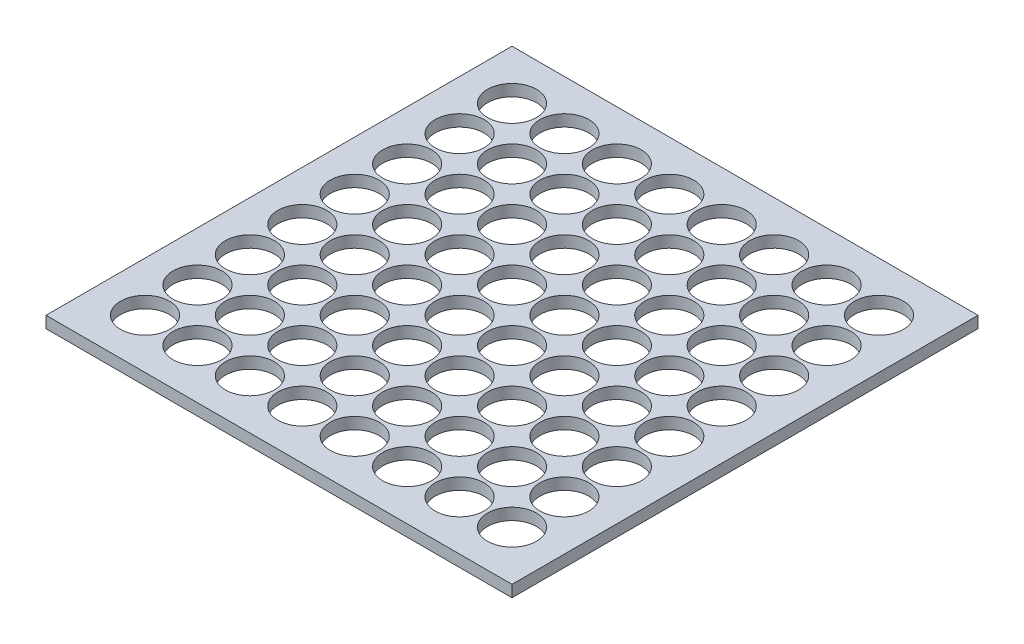
SolidWorks part; units mm, degrees
ref_plane "Front Plane" through (0, 0, 0) normal (0, 0, 1) x (1, 0, 0)
ref_plane "Top Plane" through (0, 0, 0) normal (0, 1, 0) x (1, 0, 0)
ref_plane "Right Plane" through (0, 0, 0) normal (1, 0, 0) x (0, 0, -1)
sketch "Sketch1" plane through (0, 0, 0) normal (0, 1, 0) x (1, 0, 0)
  line L0 (-189, 459) -> (189, 81) construction
  line L1 (-200, -200) -> (200, -200)
  line L2 (-200, -200) -> (-200, 200)
  line L3 (-200, 200) -> (200, 200)
  line L4 (200, -200) -> (200, 200)
  line L5 (-200, -200) -> (200, 200) construction
  line L6 (-200, 200) -> (200, -200) construction
  line L8 (-200, 470) -> (200, 70) construction
  line L9 (-189, 279) -> (189, -99) construction
  line L10 (-189, -9) -> (189, 369) construction
  line L11 (-189, -189) -> (189, 189) construction
  line L12 (-189, 189) -> (189, -189) construction
  line L13 (-189, 369) -> (189, -9) construction
  line L14 (-200, -290) -> (200, 110) construction
  line L15 (-200, -20) -> (200, 380) construction
  line L16 (-200, 380) -> (200, -20) construction
  line L17 (-189, -279) -> (189, 99) construction
  line L19 (-200, -380) -> (200, 20) construction
  line L20 (-200, 20) -> (200, -380) construction
  line L21 (-200, 290) -> (200, -110) construction
  line L22 (-189, -369) -> (189, 9) construction
  line L23 (-189, -189) -> (189, 189) construction
  line L24 (-189, 189) -> (189, -189) construction
  line L25 (-189, 9) -> (189, -369) construction
  line L26 (-200, -470) -> (200, -70) construction
  line L27 (-200, -200) -> (200, 200) construction
  line L28 (-200, 200) -> (200, -200) construction
  line L29 (-189, -459) -> (189, -81) construction
  circle A0 centre (-157.5, 157.5) radius 21
  circle A1 centre (-112.5, 157.5) radius 21
  circle A2 centre (-67.5, 157.5) radius 21
  circle A3 centre (67.5, 157.5) radius 21
  circle A4 centre (22.5, 157.5) radius 21
  circle A5 centre (-22.5, 157.5) radius 21
  circle A6 centre (112.5, 157.5) radius 21
  circle A7 centre (157.5, 157.5) radius 21
  circle A8 centre (157.5, 112.5) radius 21
  circle A9 centre (112.5, 112.5) radius 21
  circle A10 centre (-22.5, 112.5) radius 21
  circle A11 centre (22.5, 112.5) radius 21
  circle A12 centre (67.5, 112.5) radius 21
  circle A13 centre (-67.5, 112.5) radius 21
  circle A14 centre (-112.5, 112.5) radius 21
  circle A15 centre (-157.5, 112.5) radius 21
  circle A16 centre (-157.5, 67.5) radius 21
  circle A17 centre (-112.5, 67.5) radius 21
  circle A18 centre (-67.5, 67.5) radius 21
  circle A19 centre (67.5, 67.5) radius 21
  circle A20 centre (22.5, 67.5) radius 21
  circle A21 centre (-22.5, 67.5) radius 21
  circle A22 centre (112.5, 67.5) radius 21
  circle A23 centre (157.5, 67.5) radius 21
  circle A24 centre (157.5, 22.5) radius 21
  circle A25 centre (112.5, 22.5) radius 21
  circle A26 centre (-22.5, 22.5) radius 21
  circle A27 centre (22.5, 22.5) radius 21
  circle A28 centre (67.5, 22.5) radius 21
  circle A29 centre (-67.5, 22.5) radius 21
  circle A30 centre (-112.5, 22.5) radius 21
  circle A31 centre (-157.5, 22.5) radius 21
  circle A32 centre (-157.5, -22.5) radius 21
  circle A33 centre (-112.5, -22.5) radius 21
  circle A34 centre (-67.5, -22.5) radius 21
  circle A35 centre (67.5, -22.5) radius 21
  circle A36 centre (22.5, -22.5) radius 21
  circle A37 centre (-22.5, -22.5) radius 21
  circle A38 centre (112.5, -22.5) radius 21
  circle A39 centre (157.5, -22.5) radius 21
  circle A40 centre (157.5, -67.5) radius 21
  circle A41 centre (112.5, -67.5) radius 21
  circle A42 centre (-22.5, -67.5) radius 21
  circle A43 centre (22.5, -67.5) radius 21
  circle A44 centre (67.5, -67.5) radius 21
  circle A45 centre (-67.5, -67.5) radius 21
  circle A46 centre (-112.5, -67.5) radius 21
  circle A47 centre (-157.5, -67.5) radius 21
  circle A48 centre (-157.5, -112.5) radius 21
  circle A49 centre (-112.5, -112.5) radius 21
  circle A50 centre (-67.5, -112.5) radius 21
  circle A51 centre (67.5, -112.5) radius 21
  circle A52 centre (22.5, -112.5) radius 21
  circle A53 centre (-22.5, -112.5) radius 21
  circle A54 centre (112.5, -112.5) radius 21
  circle A55 centre (157.5, -112.5) radius 21
  circle A56 centre (157.5, -157.5) radius 21
  circle A57 centre (112.5, -157.5) radius 21
  circle A58 centre (-22.5, -157.5) radius 21
  circle A59 centre (22.5, -157.5) radius 21
  circle A60 centre (67.5, -157.5) radius 21
  circle A61 centre (-67.5, -157.5) radius 21
  circle A62 centre (-112.5, -157.5) radius 21
  circle A63 centre (-157.5, -157.5) radius 21
  point P0 (0, 0)
  point P6 (0, 0)
  dimension "D5" = 45
  dimension "D1" = 400
  dimension "D2" = 400
  dimension "D6" = 45
extrude "Boss-Extrude1" add sketch "Sketch1" along normal blind 10
